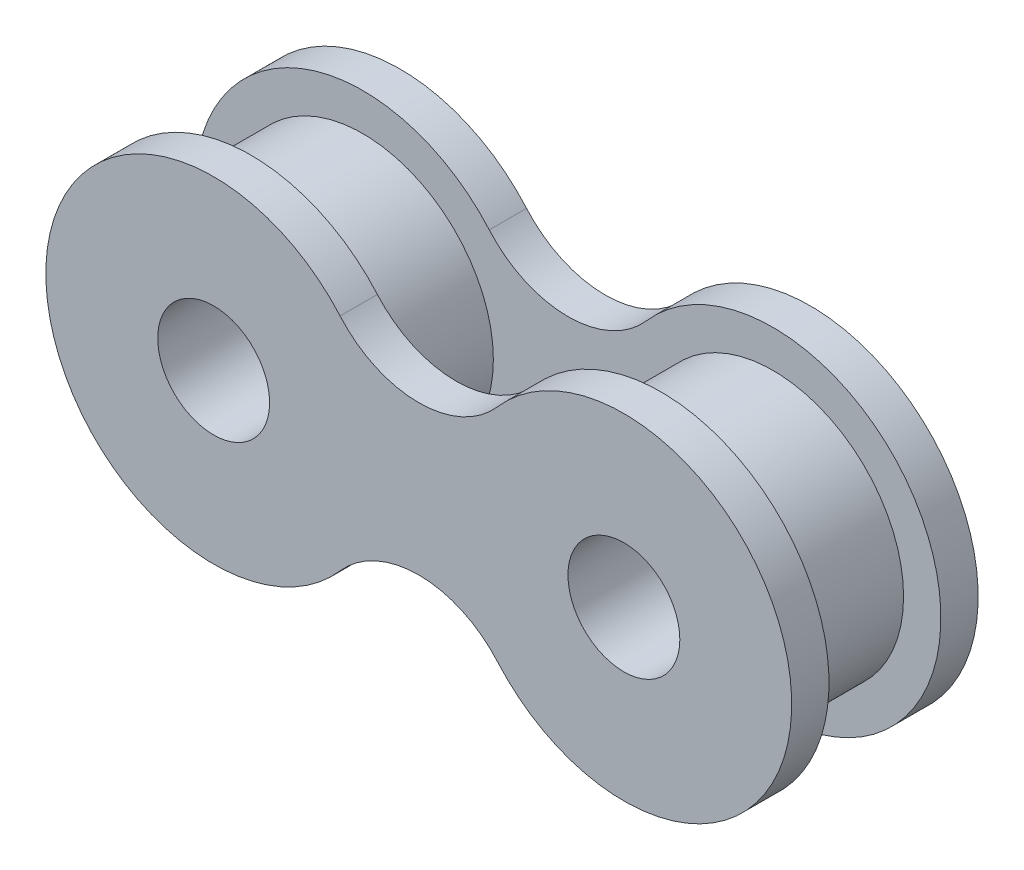
SolidWorks part; units mm, degrees
ref_plane "Alzado" through (0, 0, 0) normal (0, 0, 1) x (1, 0, 0)
ref_plane "Planta" through (0, 0, 0) normal (0, 1, 0) x (1, 0, 0)
ref_plane "Vista lateral" through (0, 0, 0) normal (1, 0, 0) x (0, 0, -1)
sketch "Croquis1" plane through (0, 0, 0) normal (0, 0, 1) x (1, 0, 0)
  line L0 (-10, 0) -> (10, 0) construction
  line L1 (0, -2) -> (0, 2) construction
  arc A0 (2.1096, -2.9589) -> (2.1096, 2.9589) centre (5.5, 0) ccw
  arc A1 (-2.1096, -2.9589) -> (-2.1096, 2.9589) centre (-5.5, 0) cw
  arc A2 (-2.1096, 2.9589) -> (2.1096, 2.9589) centre (0, 4.8) ccw
  arc A3 (-2.1096, -2.9589) -> (2.1096, -2.9589) centre (0, -4.8) cw
  circle A4 centre (-5.5, 0) radius 1.5
  circle A5 centre (5.5, 0) radius 1.5
  point P6 (0, 0)
  point P8 (10, 0)
  point P13 (0, 0)
  point P16 (0, 2)
  dimension "D1" = 9
  dimension "D4" = 3
  dimension "D2" = 20
  dimension "D3" = 4
extrude "Saliente-Extruir1" add sketch "Croquis1" along normal blind 1
sketch "Croquis2" plane through (0, 0, 1) normal (0, 0, 1) x (1, 0, 0)
  circle A0 centre (-5.5, 0) radius 3.5
  circle A1 centre (5.5, 0) radius 3.5
  circle A2 centre (5.5, 0) radius 1.5 construction
  circle A3 centre (5.5, 0) radius 1.5
  circle A4 centre (-5.5, 0) radius 1.5 construction
  circle A5 centre (-5.5, 0) radius 1.5
  dimension "D1" = 7
  dimension "D2" = 7
extrude "Saliente-Extruir2" add sketch "Croquis2" along normal blind 3
sketch "Croquis3" plane through (0, 0, 4) normal (0, 0, 1) x (1, 0, 0)
  circle A0 centre (-5.5, 0) radius 1.5 construction
  circle A1 centre (-5.5, 0) radius 1.5
  circle A2 centre (5.5, 0) radius 1.5 construction
  circle A3 centre (5.5, 0) radius 1.5
  arc A4 (-2.1096, 2.9589) -> (2.1096, 2.9589) centre (0, 4.8) ccw
  arc A5 (-2.1096, 2.9589) -> (-2.1096, -2.9589) centre (-5.5, 0) ccw
  arc A6 (2.1096, -2.9589) -> (-2.1096, -2.9589) centre (0, -4.8) ccw
  arc A7 (2.1096, -2.9589) -> (2.1096, 2.9589) centre (5.5, 0) ccw
  arc A8 (-2.1096, 2.9589) -> (2.1096, 2.9589) centre (0, 4.8) ccw
  arc A9 (-2.1096, 2.9589) -> (-2.1096, -2.9589) centre (-5.5, 0) ccw
  arc A10 (2.1096, -2.9589) -> (-2.1096, -2.9589) centre (0, -4.8) ccw
  arc A11 (2.1096, -2.9589) -> (2.1096, 2.9589) centre (5.5, 0) ccw
  dimension "D1" = 0
extrude "Saliente-Extruir3" add sketch "Croquis3" along normal blind 1
